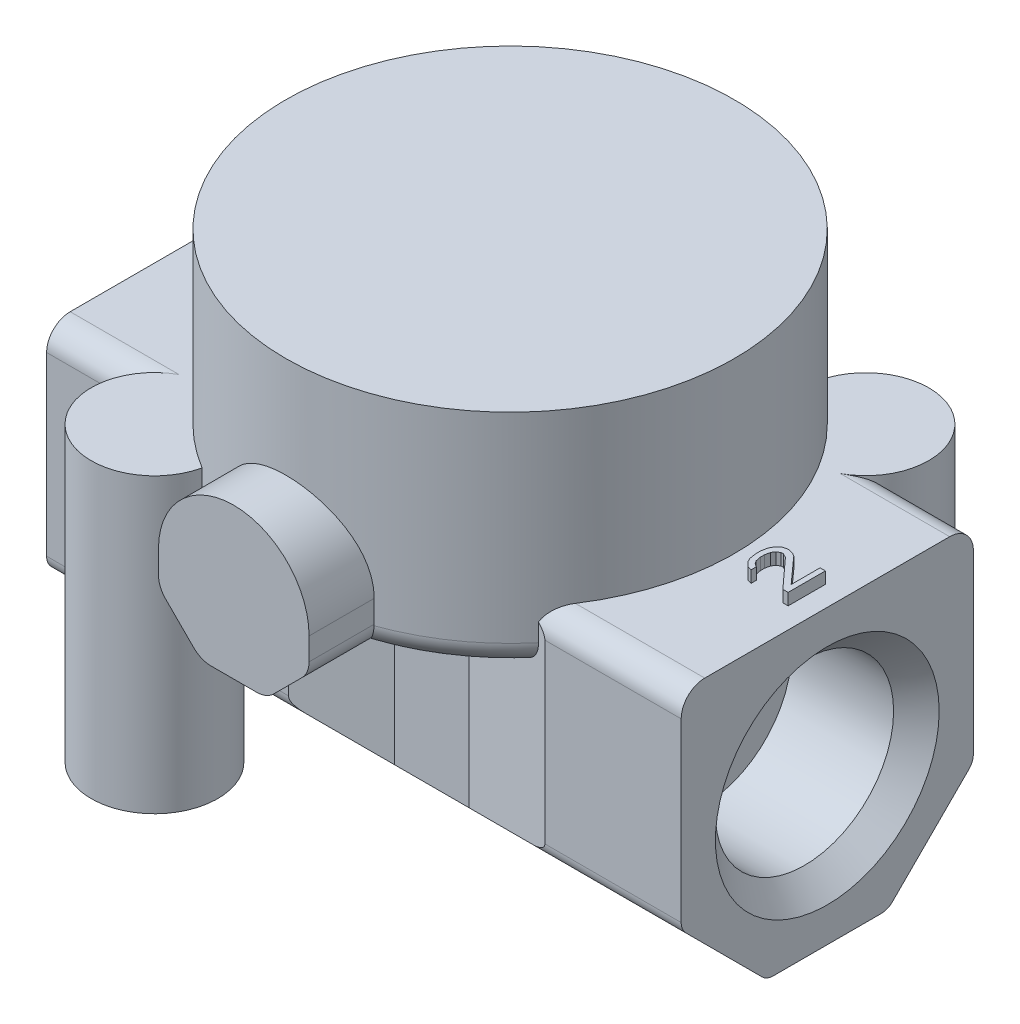
SolidWorks part; units mm, degrees
ref_plane "Front Plane" through (0, 0, 0) normal (0, 0, 1) x (1, 0, 0)
ref_plane "Top Plane" through (0, 0, 0) normal (0, 1, 0) x (1, 0, 0)
ref_plane "Right Plane" through (0, 0, 0) normal (1, 0, 0) x (0, 0, -1)
ref_plane "Plane1" through (19.8, 0, 0) normal (1, 0, 0) x (0, 0, -1)
sketch "Sketch1" plane through (19.8, 0, 0) normal (1, 0, 0) x (0, 0, -1)
  line L0 (-8.8268, -4.0864) -> (-4.0704, -8.8428)
  line L1 (-3.3633, -9.1357) -> (3.3633, -9.1357)
  line L2 (4.0704, -8.8428) -> (8.8268, -4.0864)
  line L3 (9.1197, -3.3793) -> (9.1197, 7.624)
  line L4 (7.64, 9.1037) -> (-7.65, 9.1037)
  line L5 (-9.1197, 7.634) -> (-9.1197, -3.3793)
  arc A0 (-9.1197, -3.3793) -> (-8.8268, -4.0864) centre (-8.1197, -3.3793) ccw
  arc A1 (-4.0704, -8.8428) -> (-3.3633, -9.1357) centre (-3.3633, -8.1357) ccw
  arc A2 (3.3633, -9.1357) -> (4.0704, -8.8428) centre (3.3633, -8.1357) ccw
  arc A3 (8.8268, -4.0864) -> (9.1197, -3.3793) centre (8.1197, -3.3793) ccw
  arc A4 (9.1197, 7.624) -> (7.64, 9.1037) centre (7.64, 7.624) ccw
  arc A5 (-7.65, 9.1037) -> (-9.1197, 7.634) centre (-7.65, 7.634) ccw
extrude "Boss-Extrude1" add sketch "Sketch1" against normal blind 39.612
ref_plane "Plane2" through (0, 0, 0) normal (0, 0, 1) x (1, 0, 0)
sketch "Sketch2" plane through (0, 0, 0) normal (0, 0, 1) x (1, 0, 0)
  line L0 (-11.4, -16.4478) -> (11.4, -16.4478)
  line L1 (11.4, -16.4478) -> (11.4, -9.166)
  line L2 (11.4, -9.166) -> (4.8, -7.366)
  line L3 (4.8, -7.366) -> (-4.8, -7.366)
  line L4 (-4.8, -7.366) -> (-11.4, -9.166)
  line L5 (-11.4, -9.166) -> (-11.4, -16.4478)
extrude "Cut-Extrude1" cut sketch "Sketch2" against normal blind 5.5472 and the other way blind 5.5472
ref_plane "Plane3" through (0, 0, 0) normal (0, 1, 0) x (1, 0, 0)
sketch "Sketch3" plane through (0, 0, 0) normal (0, 1, 0) x (1, 0, 0)
  line L0 (-41.3168, -33.6828) -> (43.0205, -33.6828)
  line L1 (43.0205, -33.6828) -> (43.0205, 31.7327)
  line L2 (43.0205, 31.7327) -> (-41.3168, 31.7327)
  line L3 (-41.3168, 31.7327) -> (-41.3168, -33.6828)
  line L4 (-26.1529, 16.9218) -> (-26.1529, -16.9218)
  line L5 (-26.1529, -16.9218) -> (0.1455, -7.35)
  line L6 (0.1455, -7.35) -> (4.8, -7.35)
  line L7 (4.8, -7.35) -> (30.1992, -14.2771)
  line L8 (30.1992, -14.2771) -> (30.1992, 14.2771)
  line L9 (30.1992, 14.2771) -> (4.8, 7.35)
  line L10 (4.8, 7.35) -> (0.1455, 7.35)
  line L11 (0.1455, 7.35) -> (-26.1529, 16.9218)
extrude "Cut-Extrude2" cut sketch "Sketch3" against normal blind 8.2762 and the other way blind 8.2762
ref_plane "Plane4" through (0, 0, 0) normal (1, 0, 0) x (0, 0, -1)
sketch "Sketch4" plane through (0, 0, 0) normal (1, 0, 0) x (0, 0, -1)
  line L0 (0, 19.65) -> (14, 19.65)
  line L1 (14, 19.65) -> (14, 7.15)
  line L2 (12.5, 5.65) -> (0, 5.65)
  line L3 (0, 5.65) -> (0, 19.65)
  line L4 (0, 5.65) -> (0, 19.65) construction
  arc A0 (14, 7.15) -> (12.5, 5.65) centre (12.5, 7.15) cw
revolve "Revolve1" add sketch "Sketch4" angle 360 about L4
ref_plane "Plane5" through (0, -9.166, 0) normal (0, -1, 0) x (-1, 0, 0)
sketch "Sketch5" plane through (0, -9.166, 0) normal (0, -1, 0) x (-1, 0, 0)
  circle A0 centre (11.1, -11.1) radius 3.95
extrude "Boss-Extrude2" add sketch "Sketch5" against normal blind 18.2697
ref_plane "Plane6" through (0, 0, 17.25) normal (0, 0, 1) x (1, 0, 0)
sketch "Sketch6" plane through (0, 0, 17.25) normal (0, 0, 1) x (1, 0, 0)
  line L0 (-4.7, 8.63) -> (-4.7, 7.2313)
  line L1 (-4.2536, 6.1536) -> (-2.4964, 4.3964)
  line L2 (-1.4187, 3.95) -> (1.4187, 3.95)
  line L3 (2.4964, 4.3964) -> (4.2536, 6.1536)
  line L4 (4.7, 7.2313) -> (4.7, 8.63)
  arc A0 (4.7, 8.63) -> (-4.7, 8.63) centre (0, 8.65) ccw
  arc A1 (-4.7, 7.2313) -> (-4.2536, 6.1536) centre (-3.176, 7.2313) ccw
  arc A2 (-2.4964, 4.3964) -> (-1.4187, 3.95) centre (-1.4187, 5.474) ccw
  arc A3 (1.4187, 3.95) -> (2.4964, 4.3964) centre (1.4187, 5.474) ccw
  arc A4 (4.2536, 6.1536) -> (4.7, 7.2313) centre (3.176, 7.2313) ccw
extrude "Boss-Extrude3" add sketch "Sketch6" against normal blind 20
ref_plane "Plane7" through (0, -9.166, 0) normal (0, -1, 0) x (-1, 0, 0)
sketch "Sketch7" plane through (0, -9.166, 0) normal (0, -1, 0) x (-1, 0, 0)
  circle A0 centre (-11.1, 11.1) radius 3.937
extrude "Boss-Extrude4" add sketch "Sketch7" against normal blind 18.2697
ref_plane "Plane8" through (0, 9.134, 0) normal (0, 1, 0) x (1, 0, 0)
sketch "Sketch8" plane through (0, 9.134, 0) normal (0, 1, 0) x (1, 0, 0)
  line L0 (-15.2, -0.265) -> (-15.2, 0.1225)
  line L1 (-15.2, 0.1225) -> (-15.6617, 0.51)
  line L2 (-15.6617, 0.51) -> (-16.1894, 0.51)
  line L3 (-16.1894, 0.51) -> (-15.7277, 0.1225)
  line L4 (-15.7277, 0.1225) -> (-18.3, 0.1225)
  line L5 (-18.3, 0.1225) -> (-18.3, -0.265)
  line L6 (-18.3, -0.265) -> (-15.2, -0.265)
extrude "Boss-Extrude5" add sketch "Sketch8" against normal blind 0.7 and the other way blind 0.7
ref_plane "Plane9" through (0, 9.134, 0) normal (0, 1, 0) x (1, 0, 0)
sketch "Sketch9" plane through (0, 9.134, 0) normal (0, 1, 0) x (1, 0, 0)
  line L0 (18.5, -1.143) -> (18.5, 1.182)
  line L1 (18.5, 1.182) -> (18.1702, 1.182)
  line L2 (18.1702, 1.182) -> (18.1702, -0.6263)
  line L3 (18.1702, -0.6263) -> (16.7191, 0.9882)
  line L4 (16.7191, 0.9882) -> (16.5213, 1.1174)
  line L5 (16.5213, 1.1174) -> (16.2574, 1.182)
  line L6 (16.2574, 1.182) -> (16.1255, 1.182)
  line L7 (16.1255, 1.182) -> (15.8617, 1.1174)
  line L8 (15.8617, 1.1174) -> (15.5979, 0.8591)
  line L9 (15.5979, 0.8591) -> (15.466, 0.6008)
  line L10 (15.466, 0.6008) -> (15.4, 0.2132)
  line L11 (15.4, 0.2132) -> (15.4, -0.0451)
  line L12 (15.4, -0.0451) -> (15.466, -0.4972)
  line L13 (15.466, -0.4972) -> (15.5979, -0.7555)
  line L14 (15.5979, -0.7555) -> (15.8617, -1.0138)
  line L15 (15.8617, -1.0138) -> (16.1255, -1.0784)
  line L16 (16.1255, -1.0784) -> (16.1255, -0.7555)
  line L17 (16.1255, -0.7555) -> (15.9277, -0.6263)
  line L18 (15.9277, -0.6263) -> (15.7957, -0.4326)
  line L19 (15.7957, -0.4326) -> (15.7298, -0.1097)
  line L20 (15.7298, -0.1097) -> (15.7298, 0.1487)
  line L21 (15.7298, 0.1487) -> (15.7957, 0.4716)
  line L22 (15.7957, 0.4716) -> (15.9277, 0.6653)
  line L23 (15.9277, 0.6653) -> (16.1255, 0.7945)
  line L24 (16.1255, 0.7945) -> (16.2574, 0.7945)
  line L25 (16.2574, 0.7945) -> (16.5213, 0.6653)
  line L26 (16.5213, 0.6653) -> (18.1702, -1.143)
  line L27 (18.1702, -1.143) -> (18.5, -1.143)
extrude "Boss-Extrude6" add sketch "Sketch9" against normal blind 0.7 and the other way blind 0.7
ref_plane "Plane10" through (0, 0, -11.1) normal (0, 0, -1) x (-1, 0, 0)
sketch "Sketch10" plane through (0, 0, -11.1) normal (0, 0, -1) x (-1, 0, 0)
  line L0 (-11.1125, -9.166) -> (-13.97, -9.166)
  line L1 (-13.97, -9.166) -> (-13.208, -8.404)
  line L2 (-13.208, -8.404) -> (-13.208, 0.484)
  line L3 (-13.208, 0.484) -> (-11.1125, 1.7431)
  line L4 (-11.1125, 1.7431) -> (-11.1125, -9.166)
  line L5 (-11.1125, 1.7432) -> (-11.1125, -9.166) construction
revolve "Cut-Revolve1" cut sketch "Sketch10" angle 360 about L5
ref_plane "Plane11" through (0, 0, 11.1) normal (0, 0, -1) x (-1, 0, 0)
sketch "Sketch11" plane through (0, 0, 11.1) normal (0, 0, -1) x (-1, 0, 0)
  line L0 (11.1125, -9.166) -> (8.317, -9.166)
  line L1 (8.317, -9.166) -> (9.0455, -8.4375)
  line L2 (9.0455, -8.4375) -> (9.0455, 0.5011)
  line L3 (9.0455, 0.5011) -> (11.1125, 1.7431)
  line L4 (11.1125, 1.7431) -> (11.1125, -9.166)
  line L5 (11.1125, 1.7432) -> (11.1125, -9.166) construction
revolve "Cut-Revolve2" cut sketch "Sketch11" angle 360 about L5
ref_plane "Plane12" through (0, 0, 0) normal (0, 0, -1) x (-1, 0, 0)
sketch "Sketch12" plane through (0, 0, 0) normal (0, 0, -1) x (-1, 0, 0)
  line L0 (12, 0) -> (12, 5.4991)
  line L1 (12, 5.4991) -> (18.3111, 5.4991)
  line L2 (18.3111, 5.4991) -> (19.812, 7)
  line L3 (19.812, 7) -> (19.812, 0)
  line L4 (19.812, 0) -> (12, 0)
  line L5 (19.812, 0) -> (12, 0) construction
revolve "Cut-Revolve3" cut sketch "Sketch12" angle 360 about L5
ref_plane "Plane13" through (0, 0, 0) normal (0, 0, -1) x (-1, 0, 0)
sketch "Sketch13" plane through (0, 0, 0) normal (0, 0, -1) x (-1, 0, 0)
  line L0 (-19.8, 0) -> (-19.8, 6.985)
  line L1 (-19.8, 6.985) -> (-18.3776, 5.5626)
  line L2 (-18.3776, 5.5626) -> (-12, 5.5626)
  line L3 (-12, 5.5626) -> (-12, 0)
  line L4 (-12, 0) -> (-19.8, 0)
  line L5 (-12, 0) -> (-19.8, 0) construction
revolve "Cut-Revolve4" cut sketch "Sketch13" angle 360 about L5
